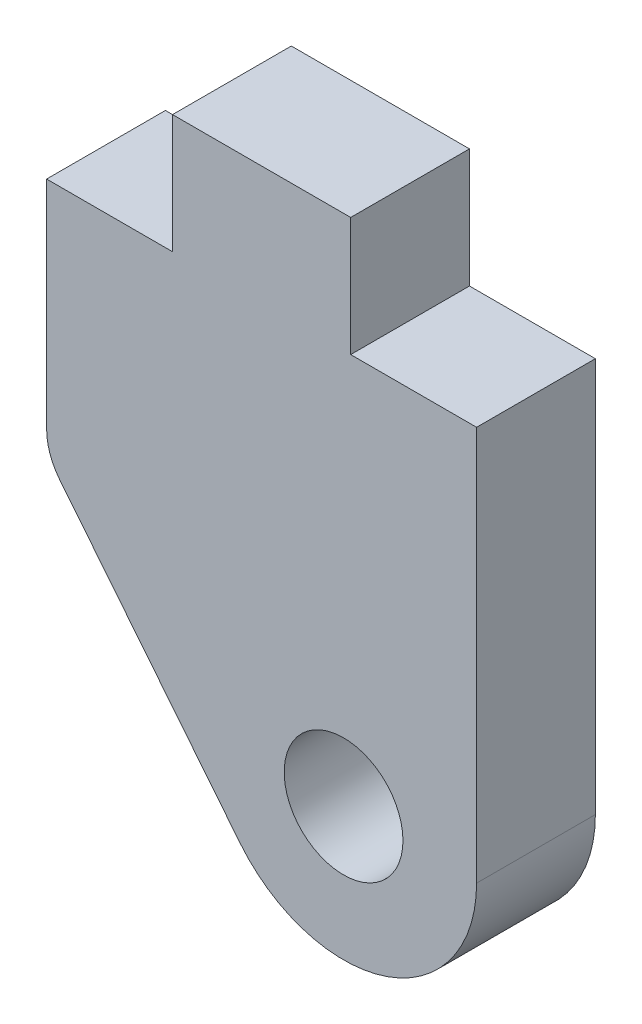
SolidWorks part; units mm, degrees
ref_plane "Front Plane" through (0, 0, 0) normal (0, 0, 1) x (1, 0, 0)
ref_plane "Top Plane" through (0, 0, 0) normal (0, 1, 0) x (1, 0, 0)
ref_plane "Right Plane" through (0, 0, 0) normal (1, 0, 0) x (0, 0, -1)
sketch "Sketch1" plane through (0, 0, 0) normal (0, 0, 1) x (1, 0, 0)
  line L0 (-5.7468, 0) -> (5.7468, 0) construction
  line L1 (-5.7468, 0) -> (-5.7467, -5.7914)
  line L2 (5.7468, 0) -> (5.7468, -10.5537)
  line L3 (-5.3969, -6.7855) -> (-0.5817, -12.7805)
  line L4 (-5.7468, 0) -> (-2.3813, 0)
  line L5 (-2.3813, 0) -> (2.3812, 0) construction
  line L6 (-2.3813, 0) -> (-2.3813, 3.175)
  line L7 (-2.3813, 3.175) -> (2.3812, 3.175)
  line L8 (2.3812, 0) -> (2.3812, 3.175)
  line L9 (2.3812, 0) -> (5.7468, 0)
  arc A0 (5.7468, -10.5537) -> (-0.5817, -12.7805) centre (2.1908, -10.5537) cw
  circle A1 centre (2.1908, -10.5537) radius 1.5875
  arc A2 (-5.3969, -6.7855) -> (-5.7467, -5.7914) centre (-4.1592, -5.7914) cw
  point P4 (0, 0)
  point P12 (-5.7467, -6.35)
  dimension "D4" = 3.556
  dimension "D5" = 3.175
  dimension "D6" = 1.5875
  dimension "D1" = 11.4935
  dimension "D2" = 6.35
  dimension "D3" = 10.5537
  dimension "D7" = 3.175
  dimension "D8" = 4.7625
  dimension "D9" = 2.3813
extrude "Boss-Extrude1" add sketch "Sketch1" along normal mid plane 3.175 contours A0 L2 L0 L1 L3 A1
equation "\"D9@Sketch1\"=\"D8@Sketch1\"/2"
